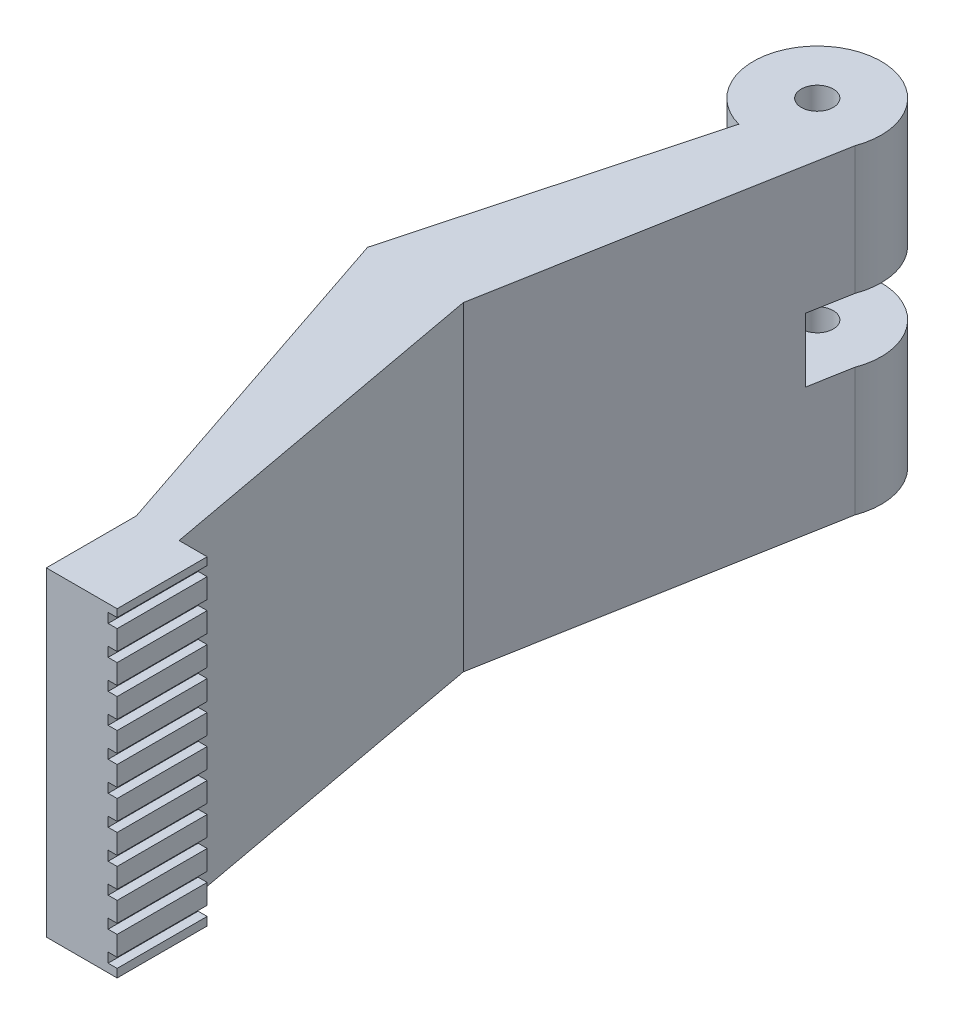
SolidWorks part; units mm, degrees
material "Ductile Iron"
ref_plane "Front Plane" through (0, 0, 0) normal (0, 0, 1) x (1, 0, 0)
ref_plane "Top Plane" through (0, 0, 0) normal (0, 1, 0) x (1, 0, 0)
ref_plane "Right Plane" through (0, 0, 0) normal (1, 0, 0) x (0, 0, -1)
sketch "Sketch1" plane through (0, 0, 0) normal (0, 1, 0) x (1, 0, 0)
  line L0 (9.3677, -3.4995) -> (0.0001, -55.3428)
  line L1 (0.0001, -55.3428) -> (10, -109.7733)
  line L3 (10, -123.8475) -> (3.3202, -123.8475)
  line L4 (3.3202, -123.8475) -> (3.3202, -109.7733)
  line L5 (3.3202, -109.7733) -> (-14.969, -55.3428)
  line L6 (-14.969, -55.3428) -> (-2.611, -9.6531)
  line L7 (10, -109.7733) -> (14.3892, -109.7733)
  line L8 (14.3892, -109.7733) -> (14.3892, -123.8475)
  line L9 (14.3892, -123.8475) -> (10, -123.8475)
  arc A0 (9.3677, -3.4995) -> (-2.611, -9.6531) centre (0, 0) ccw
  dimension "D1" = 20
extrude "Boss-Extrude1" add sketch "Sketch1" along normal blind 50
sketch "Sketch2" plane through (0, 50, 0) normal (0, 1, 0) x (1, 0, 0)
  circle A0 centre (0, 0) radius 2.5
  dimension "D1" = 5
extrude "Cut-Extrude1" cut sketch "Sketch2" against normal blind 50
sketch "Sketch3" plane through (0, 0, 0) normal (0, 0, 1) x (1, 0, 0)
  line L0 (10, 0) -> (10, 50) construction
  line L1 (30, 20) -> (-10, 20)
  line L2 (30, 20) -> (30, 30)
  line L3 (30, 30) -> (-10, 30)
  line L4 (-10, 20) -> (-10, 30)
  line L5 (30, 20) -> (-10, 30) construction
  line L6 (30, 30) -> (-10, 20) construction
  line L7 (-10, 50) -> (-10, 0) construction
  point P0 (10, 25)
  dimension "D1" = 10
extrude "Cut-Extrude2" cut sketch "Sketch3" against normal blind 50 and the other way blind 10
sketch "Sketch4" plane through (0, 0, 123.8475) normal (0, 0, 1) x (1, 0, 0)
  line L0 (14.3892, 50) -> (14.3892, 0) construction
  line L1 (14.3892, 48.8051) -> (12.9812, 48.8051)
  line L2 (14.3892, 48.8051) -> (14.3892, 47.3051)
  line L3 (14.3892, 47.3051) -> (12.9812, 47.3051)
  line L4 (12.9812, 48.8051) -> (12.9812, 47.3051)
  dimension "D1" = 1.5
extrude "Cut-Extrude3" cut sketch "Sketch4" against normal blind 50
pattern_linear "LPattern1" count 20 spacing 4.6 along (0, -1, 0) of "Cut-Extrude3"
